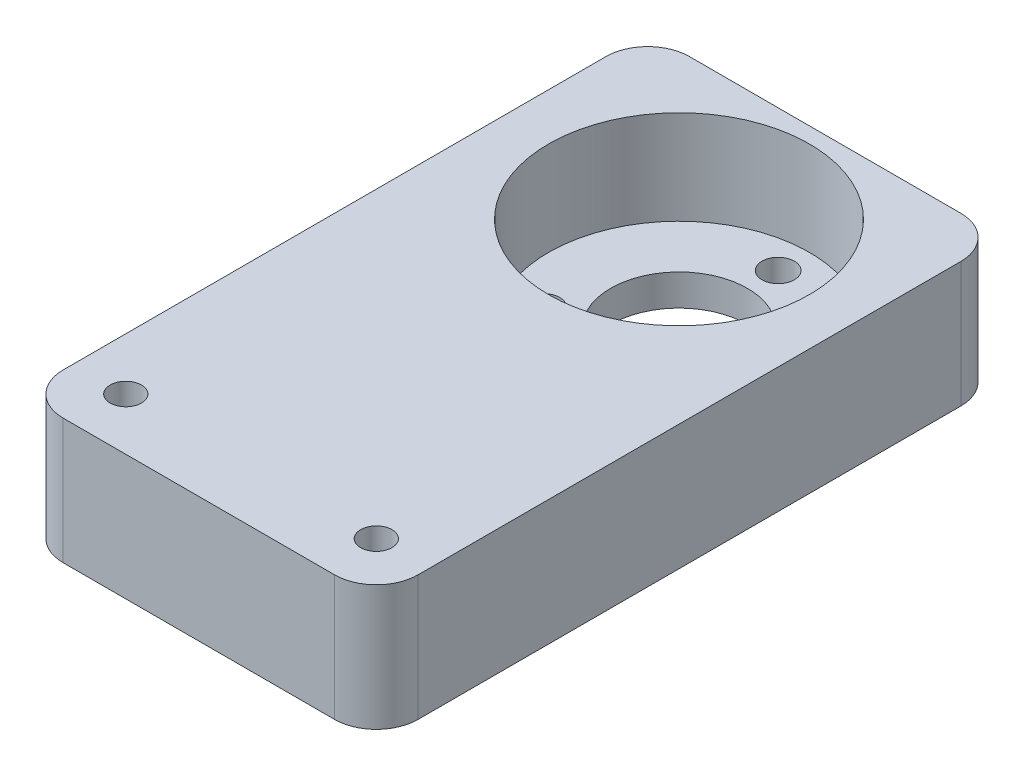
SolidWorks part; units mm, degrees
ref_plane "前视基准面" through (0, 0, 0) normal (0, 0, 1) x (1, 0, 0)
ref_plane "上视基准面" through (0, 0, 0) normal (0, 1, 0) x (1, 0, 0)
ref_plane "右视基准面" through (0, 0, 0) normal (1, 0, 0) x (0, 0, -1)
sketch "草图1" plane through (0, 0, 0) normal (0, 1, 0) x (1, 0, 0)
  line L1 (-17, -30) -> (17, -30)
  line L2 (-17, -30) -> (-17, 30)
  line L3 (-17, 30) -> (17, 30)
  line L4 (17, -30) -> (17, 30)
  line L5 (0, 30) -> (0, -30) construction
  line L6 (-17, 0) -> (17, 0) construction
  line L7 (-17, -30) -> (17, -30) construction
  line L8 (-17, -30) -> (-17, -10) construction
  line L9 (-17, -10) -> (17, -10) construction
  line L10 (17, -30) -> (17, -10) construction
  line L11 (0, -10) -> (0, -30) construction
  line L12 (-17, -20) -> (17, -20) construction
  circle A0 centre (-12, -20) radius 2.1 construction
  circle A1 centre (12, -20) radius 2.1 construction
  point P0 (0, 0)
  point P4 (0, -20)
  dimension "D4" = 4.2
  dimension "D5" = 24
  dimension "D1" = 60
  dimension "D2" = 20
  dimension "D3" = 34
extrude "主体" add sketch "草图1" along normal blind 12
sketch "草图2" plane through (0, 12, 0) normal (0, 1, 0) x (1, 0, 0)
  line L0 (-17, -30) -> (17, -30) construction
  line L1 (-17, -30) -> (17, -30) construction
  line L2 (-17, -30) -> (-17, -20) construction
  line L3 (-17, -20) -> (17, -20) construction
  line L4 (17, -30) -> (17, -20) construction
  line L5 (0, -20) -> (0, -30) construction
  line L6 (-17, -25) -> (17, -25) construction
  line L7 (-17, 30) -> (-17, -30) construction
  circle A0 centre (-12, -25) radius 2.1
  circle A1 centre (12, -25) radius 2.1
  point P0 (0, -25)
  dimension "D2" = 4.2
  dimension "D3" = 24
  dimension "D1" = 5
extrude "垂直板接件" cut sketch "草图2" against normal through all
sketch "草图3" plane through (0, 12, 0) normal (0, 1, 0) x (1, 0, 0)
  line L0 (0, -1000) -> (0, 49000) construction
  line L1 (-17, -30) -> (17, -30) construction
  circle A0 centre (0, 16) radius 12.5
  dimension "D1" = 25
  dimension "D2" = 46
extrude "沉机身" cut sketch "草图3" against normal blind 9
sketch "草图4" plane through (0, 3, 0) normal (0, 1, 0) x (1, 0, 0)
  circle A0 centre (0, 16) radius 6.55
  circle A1 centre (0, 16) radius 12.5 construction
  dimension "D1" = 13.1
extrude "电机凸台" cut sketch "草图4" against normal through all
sketch "草图5" plane through (0, 3, 0) normal (0, 1, 0) x (1, 0, 0)
  circle A0 centre (0, 16) radius 9.5 construction
  circle A1 centre (0, 16) radius 12.5 construction
  circle A2 centre (0, 25.5) radius 1.55
  circle A3 centre (8.2272, 11.25) radius 1.55
  circle A4 centre (-8.2272, 11.25) radius 1.55
  point P12 (0, 16)
  dimension "D1" = 19
  dimension "D2" = 3.1
  dimension "D3" = 3
extrude "电机固定孔" cut sketch "草图5" against normal through all
fillet "圆角4" radius 4 4 edges at (17, 6, 30) (-17, 6, 30) (17, 6, -30) (-17, 6, -30)
sketch "草图6" plane through (0, 12, 0) normal (0, 1, 0) x (1, 0, 0)
  circle A0 centre (-12, -25) radius 2.1
  circle A1 centre (-12, -25) radius 1.5
  circle A2 centre (12, -25) radius 2.1
  circle A3 centre (12, -25) radius 1.5
extrude "凸台-拉伸1" add sketch "草图6" against normal up to surface (12 mm away) up to face at (0, 0, -23.95)
